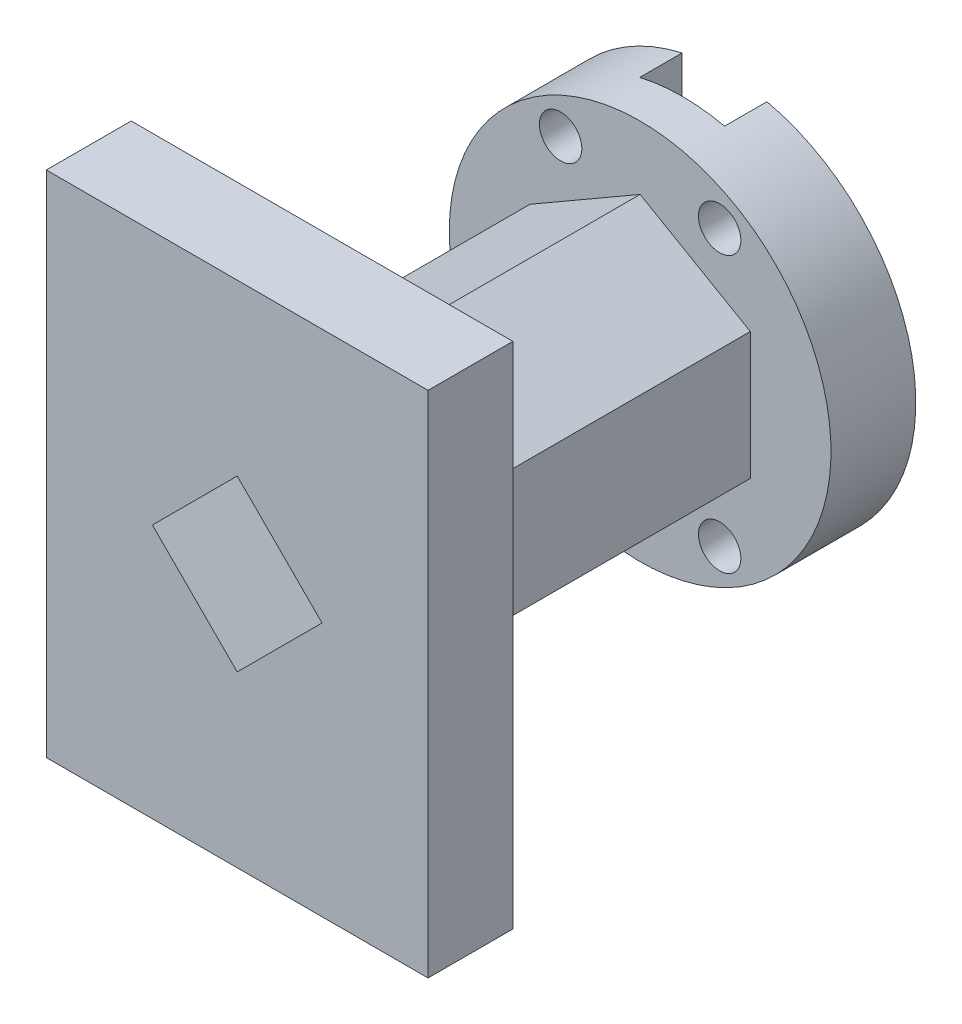
SolidWorks part; units mm, degrees
ref_plane "Спереди" through (0, 0, 0) normal (0, 0, 1) x (1, 0, 0)
ref_plane "Сверху" through (0, 0, 0) normal (0, 1, 0) x (1, 0, 0)
ref_plane "Справа" through (0, 0, 0) normal (1, 0, 0) x (0, 0, -1)
other "Configuration Table"
sketch "Sketch2" plane through (0, 0, 0) normal (0, 0, 1) x (1, 0, 0)
  line L1 (-123.0965, 97.5015) -> (-33.0965, 97.5015)
  line L2 (-123.0965, 97.5015) -> (-123.0965, -22.4985)
  line L3 (-123.0965, -22.4985) -> (-33.0965, -22.4985)
  line L4 (-33.0965, 97.5015) -> (-33.0965, -22.4985)
  line L5 (-123.0965, 97.5015) -> (-33.0965, -22.4985) construction
  line L6 (-123.0965, -22.4985) -> (-33.0965, 97.5015) construction
  line L7 (-58.0965, 37.5015) -> (-78.0965, 57.5015)
  line L8 (-78.0965, 57.5015) -> (-98.0965, 37.5015)
  line L9 (-98.0965, 37.5015) -> (-78.0965, 17.5015)
  line L10 (-78.0965, 17.5015) -> (-58.0965, 37.5015)
  circle A0 centre (-78.0965, 37.5015) radius 20 construction
  circle A1 centre (-78.0965, 37.5015) radius 14.1421 construction
  point P0 (-78.0965, 37.5015)
  dimension "D3" = 40
  dimension "D1" = 90
  dimension "D2" = 120
extrude "Boss-Extrude4" add sketch "Sketch2" along normal blind 20 contours L2 L1 L4 L3
ref_plane "Plane7" through (0, 0, 0) normal (0, 0, -1) x (-1, 0, 0)
sketch "Sketch19" plane through (0, 0, 0) normal (0, 0, -1) x (-1, 0, 0)
  line L0 (33.0965, 97.5015) -> (123.0965, -22.4985) construction
  line L2 (78.0965, 67.5015) -> (52.1157, 52.5015)
  line L3 (52.1157, 52.5015) -> (52.1157, 22.5015)
  line L4 (52.1157, 22.5015) -> (78.0965, 7.5015)
  line L5 (78.0965, 7.5015) -> (104.0772, 22.5015)
  line L6 (104.0772, 22.5015) -> (104.0772, 52.5015)
  line L7 (104.0772, 52.5015) -> (78.0965, 67.5015)
  circle A0 centre (78.0965, 37.5015) radius 30 construction
  circle A1 centre (78.0965, 37.5015) radius 25.9808 construction
  dimension "D1" = 60
extrude "Boss-Extrude5" add sketch "Sketch19" along normal blind 75 contours L3 L4 L5 L6 L7 L2
ref_plane "Plane8" through (0, 0, -75) normal (0, 0, -1) x (-1, 0, 0)
sketch "Sketch20" plane through (0, 0, -75) normal (0, 0, -1) x (-1, 0, 0)
  line L0 (78.0965, 67.5015) -> (78.0965, 7.5015)
  circle A0 centre (78.0965, 37.5015) radius 45
  dimension "D1" = 90
extrude "Boss-Extrude6" add sketch "Sketch20" along normal blind 20
ref_plane "Plane9" through (0, 0, -95) normal (0, 0, -1) x (-1, 0, 0)
sketch "Sketch21" plane through (0, 0, -95) normal (0, 0, -1) x (-1, 0, 0)
  line L1 (68.1833, -12.4287) -> (88.1833, -12.4287)
  line L2 (68.1833, -12.4287) -> (68.1833, 87.5713)
  line L3 (68.1833, 87.5713) -> (88.1833, 87.5713)
  line L4 (88.1833, -12.4287) -> (88.1833, 87.5713)
  line L5 (68.1833, -12.4287) -> (88.1833, 87.5713) construction
  line L6 (68.1833, 87.5713) -> (88.1833, -12.4287) construction
  point P17 (24.528, 37.5015)
  point P18 (139.7645, 37.5713)
  dimension "D2" = 20
  dimension "D3" = 100
extrude "Boss-Extrude8" add sketch "Sketch21" against normal blind 10 separate body contours L2 L3 L4 L1
combine bodies "Combine1" operation type subtract main body 108 bodies to subtract 110
ref_plane "Plane10" through (0, 0, -95) normal (0, 0, -1) x (-1, 0, 0)
sketch "Sketch26" plane through (0, 0, -95) normal (0, 0, -1) x (-1, 0, 0)
  line L0 (78.0965, 106.4794) -> (78.0965, -37.2328) construction
  line L1 (68.0965, -12.4985) -> (88.0965, -12.4985)
  line L2 (68.0965, -12.4985) -> (68.0965, 87.5015)
  line L3 (68.0965, 87.5015) -> (88.0965, 87.5015)
  line L4 (88.0965, -12.4985) -> (88.0965, 87.5015)
  line L5 (68.0965, -12.4985) -> (88.0965, 87.5015) construction
  line L6 (68.0965, 87.5015) -> (88.0965, -12.4985) construction
  line L7 (78.0965, 37.5015) -> (114.4258, 100.4258) construction
  line L8 (139.6777, 37.5015) -> (24.4412, 37.5015) construction
  circle A1 centre (78.0965, 37.5015) radius 37.5 construction
  circle A2 centre (59.3465, 69.9774) radius 5
  circle A3 centre (96.8465, 69.9774) radius 5
  circle A4 centre (59.3465, 5.0255) radius 5
  circle A5 centre (96.8465, 5.0255) radius 5
  circle A6 centre (78.0965, 37.5015) radius 45
  point P1 (96.8465, 69.9774)
  point P2 (96.8465, 69.9774)
  dimension "D1" = 75
  dimension "D5" = 10
  dimension "D2" = 20
  dimension "D3" = 100
  dimension "D4" = 30
extrude "Cut-Extrude2" cut sketch "Sketch26" against normal up to surface (20 mm away) contours A2 | A3 | A4 | A5 up to face at (-123.0965, 37.5015, -75)
ref_plane "Plane11" through (0, 0, 20) normal (0, 0, 1) x (1, 0, 0)
sketch "Sketch28" plane through (0, 0, 20) normal (0, 0, 1) x (1, 0, 0)
  line L0 (-123.0965, 97.5015) -> (-33.0965, -22.4985) construction
  line L2 (-58.0965, 37.5015) -> (-78.0965, 57.5015)
  line L3 (-78.0965, 57.5015) -> (-98.0965, 37.5015)
  line L4 (-98.0965, 37.5015) -> (-78.0965, 17.5015)
  line L5 (-78.0965, 17.5015) -> (-58.0965, 37.5015)
  circle A0 centre (-78.0965, 37.5015) radius 20 construction
  dimension "D1" = 40
extrude "Cut-Extrude3" cut sketch "Sketch28" against normal up to surface (115 mm away) contours L3 L4 L5 L2 up to face at (-50.6399, 37.5015, -95)
